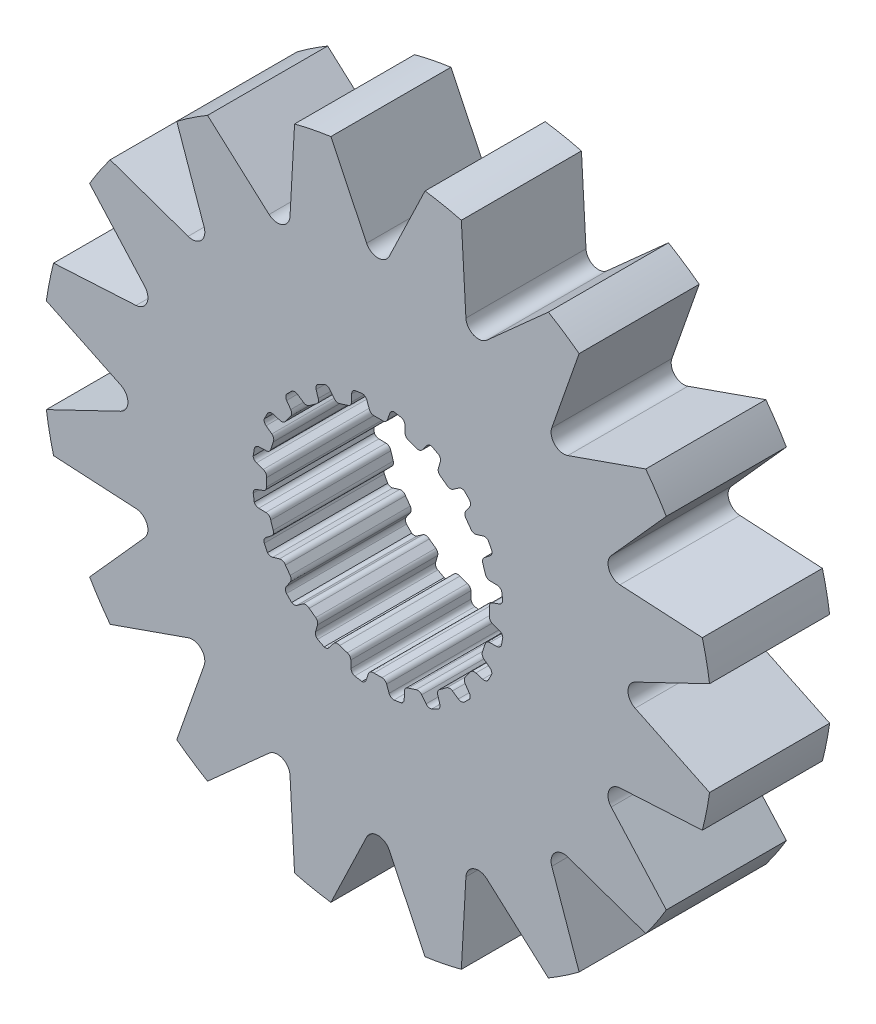
SolidWorks part; units mm, degrees
ref_plane "Front Plane" through (0, 0, 0) normal (0, 0, 1) x (1, 0, 0)
ref_plane "Top Plane" through (0, 0, 0) normal (0, 1, 0) x (1, 0, 0)
ref_plane "Right Plane" through (0, 0, 0) normal (1, 0, 0) x (0, 0, -1)
sketch "Sketch1" plane through (0, 0, 0) normal (0, 0, 1) x (1, 0, 0)
  line L0 (-0.1069, 2.9699) -> (0.1069, 2.9699)
  line L1 (0.3159, 3.2375) -> (0.2537, 3.0575)
  line L2 (-0.2964, 3.2367) -> (-0.2318, 3.0575)
  line L3 (-0.2964, 3.2367) -> (0.3159, 3.2375) construction
  line L4 (0, 3.3252) -> (0, 0) construction
  line L5 (-0.2318, 3.0575) -> (0.2537, 3.0575) construction
  line L6 (-0.4281, 3.3241) -> (0.4281, 3.3263) construction
  line L7 (0.7183, 3.1698) -> (0.7244, 2.9795)
  line L8 (0.816, 2.8576) -> (1.0195, 2.7915)
  line L9 (1.3009, 2.9815) -> (1.1862, 2.8295)
  line L10 (1.6627, 2.7927) -> (1.6097, 2.6099)
  line L11 (1.6591, 2.4655) -> (1.8322, 2.3398)
  line L12 (2.1585, 2.4335) -> (2.0025, 2.3245)
  line L13 (2.4443, 2.1423) -> (2.3374, 1.9847)
  line L14 (2.3398, 1.8322) -> (2.4655, 1.6591)
  line L15 (2.8049, 1.6474) -> (2.6228, 1.5919)
  line L16 (2.9866, 1.2821) -> (2.8363, 1.1653)
  line L17 (2.7915, 1.0195) -> (2.8576, 0.816)
  line L18 (3.1767, 0.7) -> (2.9863, 0.7035)
  line L19 (3.2367, 0.2964) -> (3.0575, 0.2318)
  line L20 (2.9699, 0.1069) -> (2.9699, -0.1069)
  line L21 (3.2375, -0.3159) -> (3.0575, -0.2537)
  line L22 (3.1698, -0.7183) -> (2.9795, -0.7244)
  line L23 (2.8576, -0.816) -> (2.7915, -1.0195)
  line L24 (2.9815, -1.3009) -> (2.8295, -1.1862)
  line L25 (2.7927, -1.6627) -> (2.6099, -1.6097)
  line L26 (2.4655, -1.6591) -> (2.3398, -1.8322)
  line L27 (2.4335, -2.1585) -> (2.3245, -2.0025)
  line L28 (2.1423, -2.4443) -> (1.9847, -2.3374)
  line L29 (1.8322, -2.3398) -> (1.6591, -2.4655)
  line L30 (1.6474, -2.8049) -> (1.5919, -2.6228)
  line L31 (1.2821, -2.9866) -> (1.1653, -2.8363)
  line L32 (1.0195, -2.7915) -> (0.816, -2.8576)
  line L33 (0.7, -3.1767) -> (0.7035, -2.9863)
  line L34 (0.2964, -3.2367) -> (0.2318, -3.0575)
  line L35 (0.1069, -2.9699) -> (-0.1069, -2.9699)
  line L36 (-0.3159, -3.2375) -> (-0.2537, -3.0575)
  line L37 (-0.7183, -3.1698) -> (-0.7244, -2.9795)
  line L38 (-0.816, -2.8576) -> (-1.0195, -2.7915)
  line L39 (-1.3009, -2.9815) -> (-1.1862, -2.8295)
  line L40 (-1.6627, -2.7927) -> (-1.6097, -2.6099)
  line L41 (-1.6591, -2.4655) -> (-1.8322, -2.3398)
  line L42 (-2.1585, -2.4335) -> (-2.0025, -2.3245)
  line L43 (-2.4443, -2.1423) -> (-2.3374, -1.9847)
  line L44 (-2.3398, -1.8322) -> (-2.4655, -1.6591)
  line L45 (-2.8049, -1.6474) -> (-2.6228, -1.5919)
  line L46 (-2.9866, -1.2821) -> (-2.8363, -1.1653)
  line L47 (-2.7915, -1.0195) -> (-2.8576, -0.816)
  line L48 (-3.1767, -0.7) -> (-2.9863, -0.7035)
  line L49 (-3.2367, -0.2964) -> (-3.0575, -0.2318)
  line L50 (-2.9699, -0.1069) -> (-2.9699, 0.1069)
  line L51 (-3.2375, 0.3159) -> (-3.0575, 0.2537)
  line L52 (-3.1698, 0.7183) -> (-2.9795, 0.7244)
  line L53 (-2.8576, 0.816) -> (-2.7915, 1.0195)
  line L54 (-2.9815, 1.3009) -> (-2.8295, 1.1862)
  line L55 (-2.7927, 1.6627) -> (-2.6099, 1.6097)
  line L56 (-2.4655, 1.6591) -> (-2.3398, 1.8322)
  line L57 (-2.4335, 2.1585) -> (-2.3245, 2.0025)
  line L58 (-2.1423, 2.4443) -> (-1.9847, 2.3374)
  line L59 (-1.8322, 2.3398) -> (-1.6591, 2.4655)
  line L60 (-1.6474, 2.8049) -> (-1.5919, 2.6228)
  line L61 (-1.2821, 2.9866) -> (-1.1653, 2.8363)
  line L62 (-1.0195, 2.7915) -> (-0.816, 2.8576)
  line L63 (-0.7, 3.1767) -> (-0.7035, 2.9863)
  line L64 (0.4281, 3.3263) -> (0.62, 3.2938)
  line L65 (1.4351, 3.0312) -> (1.6075, 2.9409)
  line L66 (2.3015, 2.4394) -> (2.4376, 2.3003)
  line L67 (2.9427, 1.6088) -> (3.0291, 1.4344)
  line L68 (3.2958, 0.6207) -> (3.3241, 0.4281)
  line L69 (3.3263, -0.4281) -> (3.2938, -0.62)
  line L70 (3.0312, -1.4351) -> (2.9409, -1.6075)
  line L71 (2.4394, -2.3015) -> (2.3003, -2.4376)
  line L72 (1.6088, -2.9427) -> (1.4344, -3.0291)
  line L73 (0.6207, -3.2958) -> (0.4281, -3.3241)
  line L74 (-0.4281, -3.3263) -> (-0.62, -3.2938)
  line L75 (-1.4351, -3.0312) -> (-1.6075, -2.9409)
  line L76 (-2.3015, -2.4394) -> (-2.4376, -2.3003)
  line L77 (-2.9427, -1.6088) -> (-3.0291, -1.4344)
  line L78 (-3.2958, -0.6207) -> (-3.3241, -0.4281)
  line L79 (-3.3263, 0.4281) -> (-3.2938, 0.62)
  line L80 (-3.0312, 1.4351) -> (-2.9409, 1.6075)
  line L81 (-2.4394, 2.3015) -> (-2.3003, 2.4376)
  line L82 (-1.6088, 2.9427) -> (-1.4344, 3.0291)
  line L83 (-0.6207, 3.2958) -> (-0.4281, 3.3241)
  arc A0 (0.2537, 3.0575) -> (0.1069, 2.9699) centre (0.1283, 3.1009) cw
  arc A1 (-0.2318, 3.0575) -> (-0.1069, 2.9699) centre (-0.1069, 3.1026) ccw
  arc A2 (0.62, 3.2938) -> (0.7183, 3.1698) centre (0.5856, 3.1656) cw
  arc A3 (0.7244, 2.9795) -> (0.816, 2.8576) centre (0.857, 2.9838) ccw
  arc A4 (-0.4281, 3.3241) -> (-0.2964, 3.2367) centre (-0.4213, 3.1916) cw
  arc A5 (0.4281, 3.3263) -> (0.3159, 3.2375) centre (0.4413, 3.1942) ccw
  arc A6 (1.1862, 2.8295) -> (1.0195, 2.7915) centre (1.0802, 2.9095) cw
  arc A7 (1.4351, 3.0312) -> (1.3009, 2.9815) centre (1.4068, 2.9015) ccw
  arc A8 (1.6075, 2.9409) -> (1.6627, 2.7927) centre (1.5352, 2.8297) cw
  arc A9 (1.6097, 2.6099) -> (1.6591, 2.4655) centre (1.7371, 2.5729) ccw
  arc A10 (2.0025, 2.3245) -> (1.8322, 2.3398) centre (1.9264, 2.4332) cw
  arc A11 (2.3015, 2.4394) -> (2.1585, 2.4335) centre (2.2346, 2.3248) ccw
  arc A12 (2.4376, 2.3003) -> (2.4443, 2.1423) centre (2.3345, 2.2168) cw
  arc A13 (2.3374, 1.9847) -> (2.3398, 1.8322) centre (2.4472, 1.9102) ccw
  arc A14 (2.6228, 1.5919) -> (2.4655, 1.6591) centre (2.5841, 1.7189) cw
  arc A15 (2.9427, 1.6088) -> (2.8049, 1.6474) centre (2.8436, 1.5205) ccw
  arc A16 (3.0291, 1.4344) -> (2.9866, 1.2821) centre (2.9052, 1.3869) cw
  arc A17 (2.8363, 1.1653) -> (2.7915, 1.0195) centre (2.9177, 1.0605) ccw
  arc A18 (2.9863, 0.7035) -> (2.8576, 0.816) centre (2.9887, 0.8362) cw
  arc A19 (3.2958, 0.6207) -> (3.1767, 0.7) centre (3.1743, 0.5673) ccw
  arc A20 (3.3241, 0.4281) -> (3.2367, 0.2964) centre (3.1916, 0.4213) cw
  arc A21 (3.0575, 0.2318) -> (2.9699, 0.1069) centre (3.1026, 0.1069) ccw
  arc A22 (3.0575, -0.2537) -> (2.9699, -0.1069) centre (3.1009, -0.1283) cw
  arc A23 (3.3263, -0.4281) -> (3.2375, -0.3159) centre (3.1942, -0.4413) ccw
  arc A24 (3.2938, -0.62) -> (3.1698, -0.7183) centre (3.1656, -0.5856) cw
  arc A25 (2.9795, -0.7244) -> (2.8576, -0.816) centre (2.9838, -0.857) ccw
  arc A26 (2.8295, -1.1862) -> (2.7915, -1.0195) centre (2.9095, -1.0802) cw
  arc A27 (3.0312, -1.4351) -> (2.9815, -1.3009) centre (2.9015, -1.4068) ccw
  arc A28 (2.9409, -1.6075) -> (2.7927, -1.6627) centre (2.8297, -1.5352) cw
  arc A29 (2.6099, -1.6097) -> (2.4655, -1.6591) centre (2.5729, -1.7371) ccw
  arc A30 (2.3245, -2.0025) -> (2.3398, -1.8322) centre (2.4332, -1.9264) cw
  arc A31 (2.4394, -2.3015) -> (2.4335, -2.1585) centre (2.3248, -2.2346) ccw
  arc A32 (2.3003, -2.4376) -> (2.1423, -2.4443) centre (2.2168, -2.3345) cw
  arc A33 (1.9847, -2.3374) -> (1.8322, -2.3398) centre (1.9102, -2.4472) ccw
  arc A34 (1.5919, -2.6228) -> (1.6591, -2.4655) centre (1.7189, -2.5841) cw
  arc A35 (1.6088, -2.9427) -> (1.6474, -2.8049) centre (1.5205, -2.8436) ccw
  arc A36 (1.4344, -3.0291) -> (1.2821, -2.9866) centre (1.3869, -2.9052) cw
  arc A37 (1.1653, -2.8363) -> (1.0195, -2.7915) centre (1.0605, -2.9177) ccw
  arc A38 (0.7035, -2.9863) -> (0.816, -2.8576) centre (0.8362, -2.9887) cw
  arc A39 (0.6207, -3.2958) -> (0.7, -3.1767) centre (0.5673, -3.1743) ccw
  arc A40 (0.4281, -3.3241) -> (0.2964, -3.2367) centre (0.4213, -3.1916) cw
  arc A41 (0.2318, -3.0575) -> (0.1069, -2.9699) centre (0.1069, -3.1026) ccw
  arc A42 (-0.2537, -3.0575) -> (-0.1069, -2.9699) centre (-0.1283, -3.1009) cw
  arc A43 (-0.4281, -3.3263) -> (-0.3159, -3.2375) centre (-0.4413, -3.1942) ccw
  arc A44 (-0.62, -3.2938) -> (-0.7183, -3.1698) centre (-0.5856, -3.1656) cw
  arc A45 (-0.7244, -2.9795) -> (-0.816, -2.8576) centre (-0.857, -2.9838) ccw
  arc A46 (-1.1862, -2.8295) -> (-1.0195, -2.7915) centre (-1.0802, -2.9095) cw
  arc A47 (-1.4351, -3.0312) -> (-1.3009, -2.9815) centre (-1.4068, -2.9015) ccw
  arc A48 (-1.6075, -2.9409) -> (-1.6627, -2.7927) centre (-1.5352, -2.8297) cw
  arc A49 (-1.6097, -2.6099) -> (-1.6591, -2.4655) centre (-1.7371, -2.5729) ccw
  arc A50 (-2.0025, -2.3245) -> (-1.8322, -2.3398) centre (-1.9264, -2.4332) cw
  arc A51 (-2.3015, -2.4394) -> (-2.1585, -2.4335) centre (-2.2346, -2.3248) ccw
  arc A52 (-2.4376, -2.3003) -> (-2.4443, -2.1423) centre (-2.3345, -2.2168) cw
  arc A53 (-2.3374, -1.9847) -> (-2.3398, -1.8322) centre (-2.4472, -1.9102) ccw
  arc A54 (-2.6228, -1.5919) -> (-2.4655, -1.6591) centre (-2.5841, -1.7189) cw
  arc A55 (-2.9427, -1.6088) -> (-2.8049, -1.6474) centre (-2.8436, -1.5205) ccw
  arc A56 (-3.0291, -1.4344) -> (-2.9866, -1.2821) centre (-2.9052, -1.3869) cw
  arc A57 (-2.8363, -1.1653) -> (-2.7915, -1.0195) centre (-2.9177, -1.0605) ccw
  arc A58 (-2.9863, -0.7035) -> (-2.8576, -0.816) centre (-2.9887, -0.8362) cw
  arc A59 (-3.2958, -0.6207) -> (-3.1767, -0.7) centre (-3.1743, -0.5673) ccw
  arc A60 (-3.3241, -0.4281) -> (-3.2367, -0.2964) centre (-3.1916, -0.4213) cw
  arc A61 (-3.0575, -0.2318) -> (-2.9699, -0.1069) centre (-3.1026, -0.1069) ccw
  arc A62 (-3.0575, 0.2537) -> (-2.9699, 0.1069) centre (-3.1009, 0.1283) cw
  arc A63 (-3.3263, 0.4281) -> (-3.2375, 0.3159) centre (-3.1942, 0.4413) ccw
  arc A64 (-3.2938, 0.62) -> (-3.1698, 0.7183) centre (-3.1656, 0.5856) cw
  arc A65 (-2.9795, 0.7244) -> (-2.8576, 0.816) centre (-2.9838, 0.857) ccw
  arc A66 (-2.8295, 1.1862) -> (-2.7915, 1.0195) centre (-2.9095, 1.0802) cw
  arc A67 (-3.0312, 1.4351) -> (-2.9815, 1.3009) centre (-2.9015, 1.4068) ccw
  arc A68 (-2.9409, 1.6075) -> (-2.7927, 1.6627) centre (-2.8297, 1.5352) cw
  arc A69 (-2.6099, 1.6097) -> (-2.4655, 1.6591) centre (-2.5729, 1.7371) ccw
  arc A70 (-2.3245, 2.0025) -> (-2.3398, 1.8322) centre (-2.4332, 1.9264) cw
  arc A71 (-2.4394, 2.3015) -> (-2.4335, 2.1585) centre (-2.3248, 2.2346) ccw
  arc A72 (-2.3003, 2.4376) -> (-2.1423, 2.4443) centre (-2.2168, 2.3345) cw
  arc A73 (-1.9847, 2.3374) -> (-1.8322, 2.3398) centre (-1.9102, 2.4472) ccw
  arc A74 (-1.5919, 2.6228) -> (-1.6591, 2.4655) centre (-1.7189, 2.5841) cw
  arc A75 (-1.6088, 2.9427) -> (-1.6474, 2.8049) centre (-1.5205, 2.8436) ccw
  arc A76 (-1.4344, 3.0291) -> (-1.2821, 2.9866) centre (-1.3869, 2.9052) cw
  arc A77 (-1.1653, 2.8363) -> (-1.0195, 2.7915) centre (-1.0605, 2.9177) ccw
  arc A78 (-0.7035, 2.9863) -> (-0.816, 2.8576) centre (-0.8362, 2.9887) cw
  arc A79 (-0.6207, 3.2958) -> (-0.7, 3.1767) centre (-0.5673, 3.1743) ccw
  circle A80 centre (0, 0) radius 8.9262
  point P14 (0, 2.9699)
  point P247 (0, 0)
  dimension "D4" = 0.1327
  dimension "D8" = 20
  dimension "D9" = 17.8524
  dimension "D1" = 2.9699
  dimension "D2" = 0.2139
  dimension "D3" = 0.1904
  dimension "D5" = 0.0877
  dimension "D6" = 0.4855
  dimension "D7" = 0.8563
extrude "Boss-Extrude1" add sketch "Sketch1" along normal mid plane 3.2004
sketch "Sketch2" plane through (0, 0, 1.6002) normal (0, 0, 1) x (1, 0, 0)
  line L0 (0, 8.8375) -> (0, 0) construction
  line L1 (1.557, 15.6914) -> (0, 0) construction
  line L2 (-1.2551, 8.8375) -> (1.2551, 8.8375) construction
  line L3 (-0.7785, 7.8457) -> (0.7785, 7.8457) construction
  line L4 (-1.2551, 8.8375) -> (-0.3019, 6.8539)
  line L5 (1.2551, 8.8375) -> (0.3019, 6.8539)
  line L6 (4.5416, 7.6845) -> (2.9018, 6.2167)
  line L7 (2.2224, 8.6451) -> (2.344, 6.4477)
  line L8 (7.1366, 5.3616) -> (5.0599, 4.633)
  line L9 (5.3616, 7.1366) -> (4.633, 5.0599)
  line L10 (8.6451, 2.2224) -> (6.4477, 2.344)
  line L11 (7.6845, 4.5416) -> (6.2167, 2.9018)
  line L12 (8.8375, -1.2551) -> (6.8539, -0.3019)
  line L13 (8.8375, 1.2551) -> (6.8539, 0.3019)
  line L14 (7.6845, -4.5416) -> (6.2167, -2.9018)
  line L15 (8.6451, -2.2224) -> (6.4477, -2.344)
  line L16 (5.3616, -7.1366) -> (4.633, -5.0599)
  line L17 (7.1366, -5.3616) -> (5.0599, -4.633)
  line L18 (2.2224, -8.6451) -> (2.344, -6.4477)
  line L19 (4.5416, -7.6845) -> (2.9018, -6.2167)
  line L20 (-1.2551, -8.8375) -> (-0.3019, -6.8539)
  line L21 (1.2551, -8.8375) -> (0.3019, -6.8539)
  line L22 (-4.5416, -7.6845) -> (-2.9018, -6.2167)
  line L23 (-2.2224, -8.6451) -> (-2.344, -6.4477)
  line L24 (-7.1366, -5.3616) -> (-5.0599, -4.633)
  line L25 (-5.3616, -7.1366) -> (-4.633, -5.0599)
  line L26 (-8.6451, -2.2224) -> (-6.4477, -2.344)
  line L27 (-7.6845, -4.5416) -> (-6.2167, -2.9018)
  line L28 (-8.8375, 1.2551) -> (-6.8539, 0.3019)
  line L29 (-8.8375, -1.2551) -> (-6.8539, -0.3019)
  line L30 (-7.6845, 4.5416) -> (-6.2167, 2.9018)
  line L31 (-8.6451, 2.2224) -> (-6.4477, 2.344)
  line L32 (-5.3616, 7.1366) -> (-4.633, 5.0599)
  line L33 (-7.1366, 5.3616) -> (-5.0599, 4.633)
  line L34 (-2.2224, 8.6451) -> (-2.344, 6.4477)
  line L35 (-4.5416, 7.6845) -> (-2.9018, 6.2167)
  circle A0 centre (0, 0) radius 8.9262 construction
  arc A1 (-0.3019, 6.8539) -> (0.3019, 6.8539) centre (0, 6.999) ccw
  arc A2 (-1.2551, 8.8375) -> (1.2551, 8.8375) centre (0, 0) cw
  arc A3 (2.2224, 8.6451) -> (4.5416, 7.6845) centre (0, 0) cw
  arc A4 (2.344, 6.4477) -> (2.9018, 6.2167) centre (2.6784, 6.4662) ccw
  arc A5 (5.3616, 7.1366) -> (7.1366, 5.3616) centre (0, 0) cw
  arc A6 (4.633, 5.0599) -> (5.0599, 4.633) centre (4.949, 4.949) ccw
  arc A7 (7.6845, 4.5416) -> (8.6451, 2.2224) centre (0, 0) cw
  arc A8 (6.2167, 2.9018) -> (6.4477, 2.344) centre (6.4662, 2.6784) ccw
  arc A9 (8.8375, 1.2551) -> (8.8375, -1.2551) centre (0, 0) cw
  arc A10 (6.8539, 0.3019) -> (6.8539, -0.3019) centre (6.999, 0) ccw
  arc A11 (8.6451, -2.2224) -> (7.6845, -4.5416) centre (0, 0) cw
  arc A12 (6.4477, -2.344) -> (6.2167, -2.9018) centre (6.4662, -2.6784) ccw
  arc A13 (7.1366, -5.3616) -> (5.3616, -7.1366) centre (0, 0) cw
  arc A14 (5.0599, -4.633) -> (4.633, -5.0599) centre (4.949, -4.949) ccw
  arc A15 (4.5416, -7.6845) -> (2.2224, -8.6451) centre (0, 0) cw
  arc A16 (2.9018, -6.2167) -> (2.344, -6.4477) centre (2.6784, -6.4662) ccw
  arc A17 (1.2551, -8.8375) -> (-1.2551, -8.8375) centre (0, 0) cw
  arc A18 (0.3019, -6.8539) -> (-0.3019, -6.8539) centre (0, -6.999) ccw
  arc A19 (-2.2224, -8.6451) -> (-4.5416, -7.6845) centre (0, 0) cw
  arc A20 (-2.344, -6.4477) -> (-2.9018, -6.2167) centre (-2.6784, -6.4662) ccw
  arc A21 (-5.3616, -7.1366) -> (-7.1366, -5.3616) centre (0, 0) cw
  arc A22 (-4.633, -5.0599) -> (-5.0599, -4.633) centre (-4.949, -4.949) ccw
  arc A23 (-7.6845, -4.5416) -> (-8.6451, -2.2224) centre (0, 0) cw
  arc A24 (-6.2167, -2.9018) -> (-6.4477, -2.344) centre (-6.4662, -2.6784) ccw
  arc A25 (-8.8375, -1.2551) -> (-8.8375, 1.2551) centre (0, 0) cw
  arc A26 (-6.8539, -0.3019) -> (-6.8539, 0.3019) centre (-6.999, 0) ccw
  arc A27 (-8.6451, 2.2224) -> (-7.6845, 4.5416) centre (0, 0) cw
  arc A28 (-6.4477, 2.344) -> (-6.2167, 2.9018) centre (-6.4662, 2.6784) ccw
  arc A29 (-7.1366, 5.3616) -> (-5.3616, 7.1366) centre (0, 0) cw
  arc A30 (-5.0599, 4.633) -> (-4.633, 5.0599) centre (-4.949, 4.949) ccw
  arc A31 (-4.5416, 7.6845) -> (-2.2224, 8.6451) centre (0, 0) cw
  arc A32 (-2.9018, 6.2167) -> (-2.344, 6.4477) centre (-2.6784, 6.4662) ccw
  point P9 (0, 7.8457)
  point P132 (0, 0)
  dimension "D1" = 0.9918
  dimension "D2" = 1.557
  dimension "D3" = 20
  dimension "D4" = 16
extrude "Cut-Extrude1" cut sketch "Sketch2" against normal up to surface (3.2004 mm away) up to face at (8.9262, 0, -1.6002)
sketch "Sketch3" plane through (0, 0, 1.6002) normal (0, 0, 1) x (1, 0, 0)
  circle A0 centre (0, 0) radius 7.9344 construction
  circle A1 centre (0, 0) radius 8.9262 construction
  dimension "D1" = 15.8688
